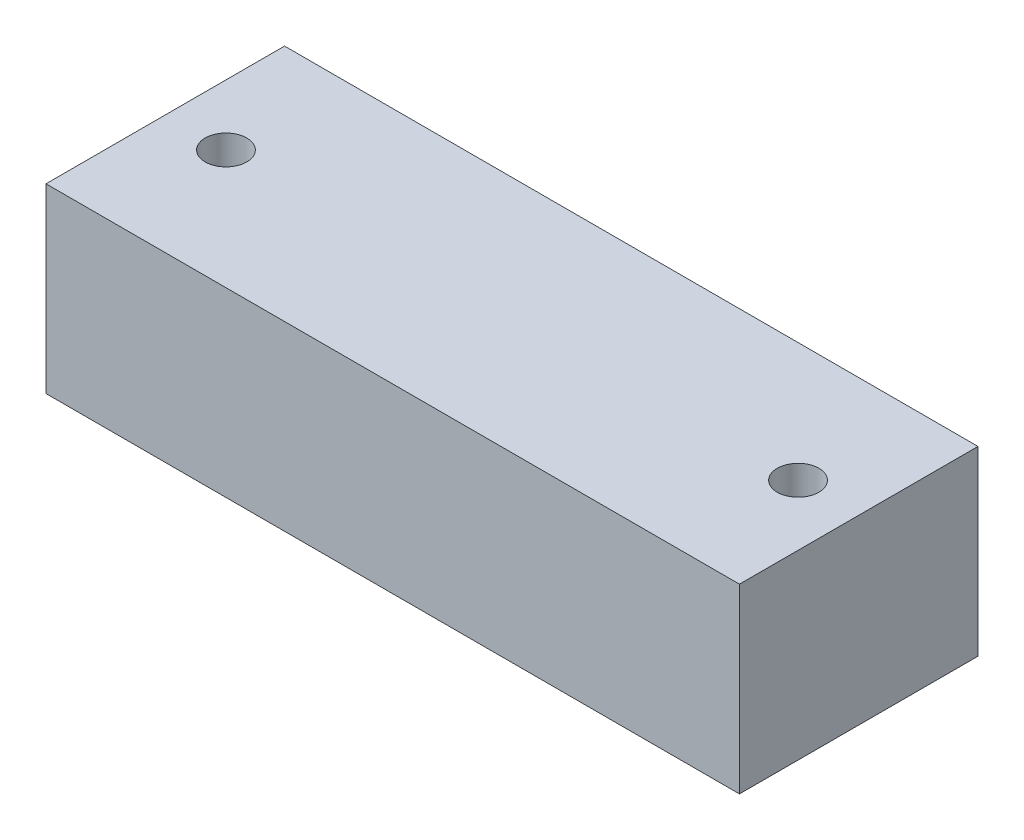
SolidWorks part; units mm, degrees
ref_plane "Front" through (0, 0, 0) normal (0, 0, 1) x (1, 0, 0)
ref_plane "Top" through (0, 0, 0) normal (0, 1, 0) x (1, 0, 0)
ref_plane "Right" through (0, 0, 0) normal (1, 0, 0) x (0, 0, -1)
sketch "Sketch1" plane through (0, 0, 0) normal (0, 1, 0) x (1, 0, 0)
  line L0 (0, 10.922) -> (5.5563, 10.922) construction
  line L1 (0, 0) -> (63.5, 0)
  line L2 (0, 0) -> (0, 21.844)
  line L3 (0, 21.844) -> (63.5, 21.844)
  line L4 (63.5, 0) -> (63.5, 21.844)
  line L5 (5.5563, 10.922) -> (57.9438, 10.922) construction
  line L6 (57.9438, 10.922) -> (63.5, 10.922) construction
  circle A0 centre (5.5563, 10.922) radius 1.905
  circle A1 centre (57.9438, 10.922) radius 1.905
  dimension "D1" = 63.5
  dimension "D4" = 3.81
  dimension "D2" = 21.844
  dimension "D3" = 52.3875
extrude "Boss-Extrude1" add sketch "Sketch1" along normal blind 16.637
